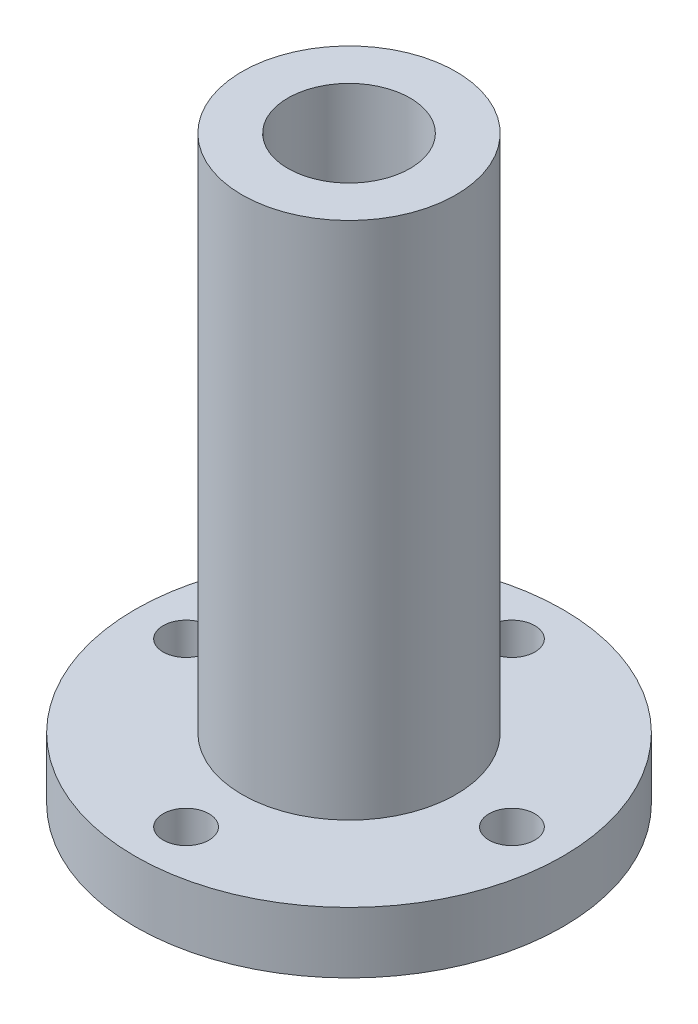
SolidWorks part; units mm, degrees
ref_plane "Front Plane" through (0, 0, 0) normal (0, 0, 1) x (1, 0, 0)
ref_plane "Top Plane" through (0, 0, 0) normal (0, 1, 0) x (1, 0, 0)
ref_plane "Right Plane" through (0, 0, 0) normal (1, 0, 0) x (0, 0, -1)
sketch "Sketch1" plane through (0, 0, 0) normal (0, 1, 0) x (1, 0, 0)
  circle A0 centre (0, 0) radius 6
  circle A1 centre (0, 0) radius 21
  dimension "D1" = 12
  dimension "D2" = 42
extrude "Boss-Extrude1" add sketch "Sketch1" along normal blind 6
sketch "Sketch2" plane through (0, 6, 0) normal (0, 1, 0) x (1, 0, 0)
  circle A0 centre (0, 0) radius 6
  circle A1 centre (0, 0) radius 10.5
  dimension "D1" = 21
extrude "Boss-Extrude2" add sketch "Sketch2" along normal blind 51
sketch "Sketch3" plane through (0, 0, 0) normal (0, -1, 0) x (1, 0, 0)
  circle A0 centre (0, 0) radius 16
  circle A1 centre (0, 16) radius 2.25
  circle A2 centre (16, 0) radius 2.25
  circle A3 centre (0, -16) radius 2.25
  circle A4 centre (-16, 0) radius 2.25
  dimension "D1" = 32
  dimension "D2" = 4.5
  dimension "D3" = 4.5
  dimension "D4" = 4.5
  dimension "D5" = 4.5
extrude "Cut-Extrude1" cut sketch "Sketch3" against normal up to next contours A0 A4 | A0 A4 | A0 A1 | A0 A1 | A0 A2 | A0 A2 | A0 A3 | A0 A3
